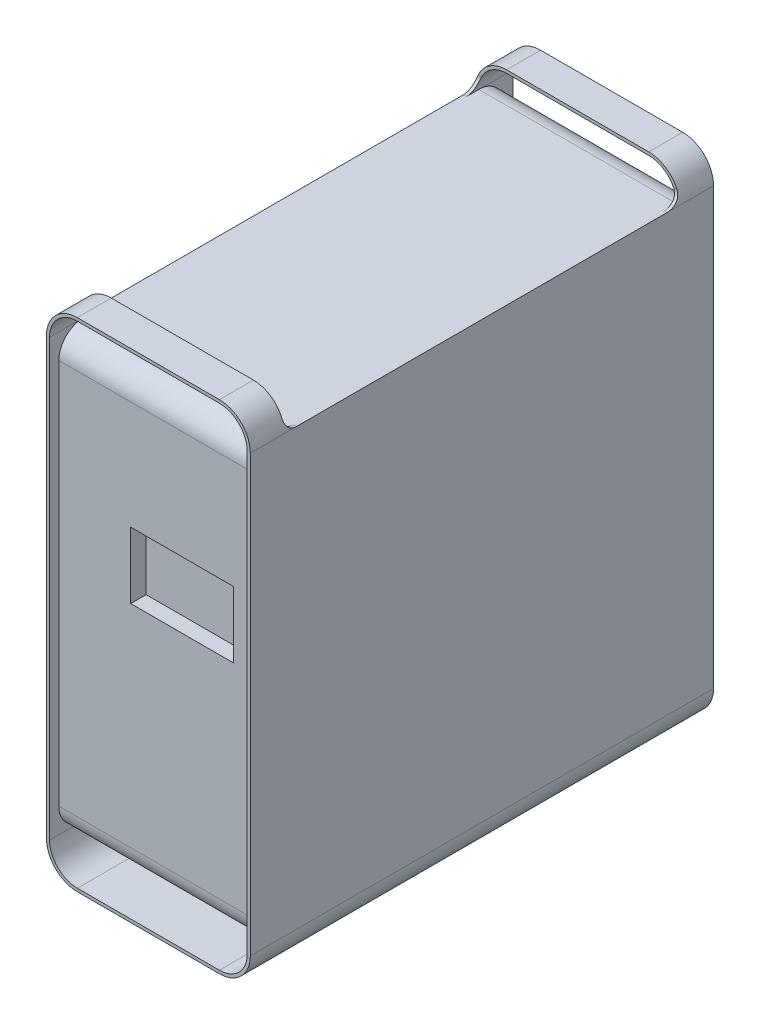
SolidWorks part; units mm, degrees
ref_plane "Front" through (0, 0, 0) normal (0, 0, 1) x (1, 0, 0)
ref_plane "Top" through (0, 0, 0) normal (0, 1, 0) x (1, 0, 0)
ref_plane "Right" through (0, 0, 0) normal (1, 0, 0) x (0, 0, -1)
sketch "Sketch1" plane through (0, 0, 0) normal (0, 0, 1) x (1, 0, 0)
  line L0 (-101.6, 223.8375) -> (-101.6, -223.8375)
  line L1 (-73.025, 255.5875) -> (73.025, 255.5875)
  line L2 (-104.775, 223.8375) -> (-104.775, -223.8375)
  line L3 (-73.025, -255.5875) -> (73.025, -255.5875)
  line L4 (104.775, 223.8375) -> (104.775, -223.8375)
  line L5 (-73.025, -252.4125) -> (73.025, -252.4125)
  line L6 (101.6, 223.8375) -> (101.6, -223.8375)
  line L7 (-73.025, 252.4125) -> (73.025, 252.4125)
  line L16 (-101.6, 0) -> (101.6, 0) construction
  line L17 (0, -252.4125) -> (0, 252.4125) construction
  arc A0 (-73.025, 255.5875) -> (-104.775, 223.8375) centre (-73.025, 223.8375) ccw
  arc A1 (73.025, 255.5875) -> (104.775, 223.8375) centre (73.025, 223.8375) cw
  arc A2 (-101.6, 223.8375) -> (-73.025, 252.4125) centre (-73.025, 223.8375) cw
  arc A3 (73.025, 252.4125) -> (101.6, 223.8375) centre (73.025, 223.8375) cw
  arc A4 (-73.025, -252.4125) -> (-101.6, -223.8375) centre (-73.025, -223.8375) cw
  arc A5 (101.6, -223.8375) -> (73.025, -252.4125) centre (73.025, -223.8375) cw
  arc A6 (-73.025, -255.5875) -> (-104.775, -223.8375) centre (-73.025, -223.8375) cw
  arc A7 (104.775, -223.8375) -> (73.025, -255.5875) centre (73.025, -223.8375) cw
  point P11 (-104.775, 255.5875)
  dimension "D4" = 31.75
  dimension "D5" = 28.575
  dimension "D6" = 31.75
  dimension "D1" = 104.775
  dimension "D2" = 255.5875
extrude "Extrude1" add sketch "Sketch1" against normal blind 476.25
sketch "Sketch2" plane through (104.775, 0, 0) normal (1, 0, 0) x (0, 0, -1)
  line L0 (476.25, 223.8375) -> (0, 223.8375) construction
  line L1 (476.25, 223.8375) -> (0, 223.8375) construction
  line L2 (34.925, 236.5375) -> (34.925, 258.5958)
  line L3 (34.925, 258.5958) -> (441.325, 258.5958)
  line L4 (441.325, 258.5958) -> (441.325, 236.5375)
  line L5 (47.625, 223.8375) -> (428.625, 223.8375)
  arc A0 (47.625, 223.8375) -> (34.925, 236.5375) centre (47.625, 236.5375) cw
  arc A1 (441.325, 236.5375) -> (428.625, 223.8375) centre (428.625, 236.5375) cw
  point P8 (34.925, 223.8375)
  point P11 (441.325, 223.8375)
  dimension "D3" = 12.7
  dimension "D1" = 34.925
  dimension "D2" = 34.925
extrude "Cut-Extrude1" cut sketch "Sketch2" against normal through all
sketch "Sketch4" plane through (-101.6, 0, 0) normal (1, 0, 0) x (0, 0, -1)
  line L0 (9.525, 198.4375) -> (9.525, -198.4375)
  line L1 (466.725, -198.4375) -> (466.725, 198.4375)
  line L2 (9.525, 223.8375) -> (9.525, -223.8375) construction
  line L3 (466.725, -223.8375) -> (466.725, 223.8375) construction
  line L6 (0, 223.8375) -> (0, -223.8375)
  line L7 (0, -223.8375) -> (476.25, -223.8375)
  line L8 (476.25, -223.8375) -> (476.25, 223.8375)
  line L9 (476.25, 223.8375) -> (428.625, 223.8375)
  line L10 (428.625, 223.8375) -> (47.625, 223.8375)
  line L11 (47.625, 223.8375) -> (0, 223.8375)
  line L12 (0, 223.8375) -> (0, -223.8375) construction
  line L13 (34.925, -223.8375) -> (441.325, -223.8375)
  line L14 (476.25, -223.8375) -> (476.25, 223.8375) construction
  line L16 (441.325, 223.8375) -> (34.925, 223.8375)
  arc A0 (9.525, 198.4375) -> (34.925, 223.8375) centre (34.925, 198.4375) cw
  arc A1 (466.725, 198.4375) -> (441.325, 223.8375) centre (441.325, 198.4375) ccw
  arc A2 (441.325, -223.8375) -> (466.725, -198.4375) centre (441.325, -198.4375) ccw
  arc A3 (34.925, -223.8375) -> (9.525, -198.4375) centre (34.925, -198.4375) cw
  dimension "D4" = 25.4
  dimension "D1" = 0
  dimension "D2" = 9.525
  dimension "D3" = 9.525
extrude "Extrude2" add sketch "Sketch4" along normal blind 203.2
sketch "Sketch5" plane through (0, 0, -9.525) normal (0, 0, 1) x (1, 0, 0)
  line L0 (-27.7267, 86.9784) -> (77.9545, 86.9784)
  line L1 (-27.7267, 18.914) -> (77.9545, 18.914)
  line L2 (-27.7267, 86.9784) -> (-27.7267, 18.914)
  line L4 (77.9545, 86.9784) -> (77.9545, 18.914)
extrude "Cut-Extrude2" cut sketch "Sketch5" against normal blind 15.875
